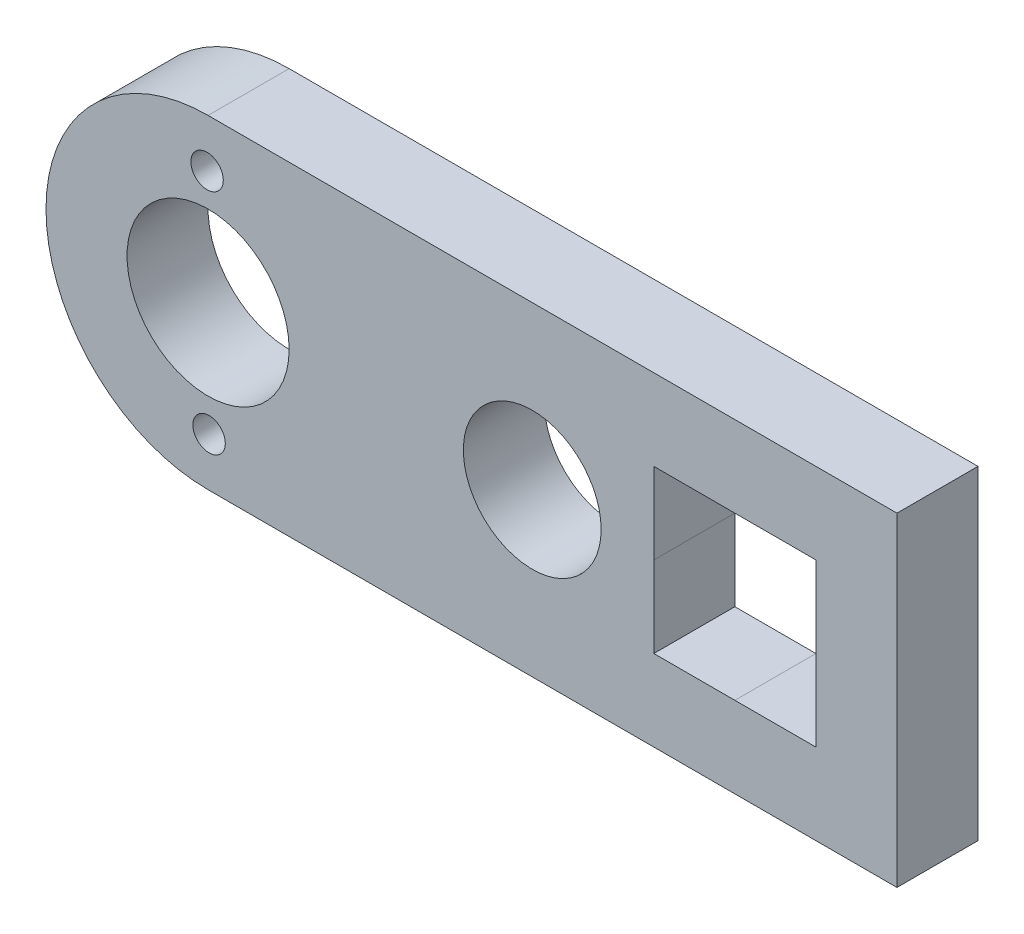
SolidWorks part; units mm, degrees
ref_plane "Front Plane" through (0, 0, 0) normal (0, 0, 1) x (1, 0, 0)
ref_plane "Top Plane" through (0, 0, 0) normal (0, 1, 0) x (1, 0, 0)
ref_plane "Right Plane" through (0, 0, 0) normal (1, 0, 0) x (0, 0, -1)
sketch "Sketch1" plane through (0, 0, 0) normal (0, 0, 1) x (1, 0, 0)
  line L0 (0, 10) -> (42.5, 10)
  line L1 (0, -10) -> (42.5, -10)
  line L2 (42.5, 10) -> (42.5, -10)
  line L3 (20, 5) -> (20, -5) construction
  line L4 (27.5, 5) -> (32.5, 5)
  line L5 (27.5, 5) -> (27.5, 0)
  line L6 (27.5, 0) -> (32.5, 0)
  line L7 (32.5, 5) -> (32.5, 0)
  line L8 (27.5, 5) -> (32.5, 0) construction
  line L9 (27.5, 0) -> (32.5, 5) construction
  line L10 (27.5, 0) -> (32.5, 0)
  line L11 (27.5, 0) -> (27.5, -5)
  line L12 (27.5, -5) -> (32.5, -5)
  line L13 (32.5, 0) -> (32.5, -5)
  line L14 (27.5, 0) -> (32.5, -5) construction
  line L15 (27.5, -5) -> (32.5, 0) construction
  line L16 (32.5, -5) -> (32.5, 5)
  line L17 (32.5, -5) -> (37.5, -5)
  line L18 (32.5, 5) -> (37.5, 5)
  line L19 (37.5, -5) -> (37.5, 5)
  arc A1 (0, 10) -> (0, -10) centre (0, 0) ccw
  circle A3 centre (20, 0) radius 4.25
  point P8 (30, 2.5)
  point P13 (30, -2.5)
  circle B0 centre (0, 0) radius 5
  circle B1 centre (7, 0.0625) radius 1
  circle B2 centre (0.0625, -7) radius 1
  circle B3 centre (-7, -0.0625) radius 1
  circle B4 centre (-0.0625, 7) radius 1
  dimension "D2" = 20
  dimension "D3" = 8.5
  dimension "D5" = 20
  dimension "D7" = 22.5
  dimension "D9" = 10
  dimension "D4" = 5
  dimension "D6" = 5
  dimension "D8" = 10
  dimension "D10" = 5
  dimension "D11" = 42.5
sketch_block_instance "Block1-1"
sketch_block "Block1" parameters "D1"=2, "D2"=10
extrude "Boss-Extrude1" add sketch "Sketch1" along normal blind 5
sketch "Sketch2" plane through (0, 0, 0) normal (0, 0, -1) x (-1, 0, 0)
  circle A0 centre (7, -0.0625) radius 1
  circle A1 centre (-7, 0.0625) radius 1.224
extrude "Boss-Extrude2" add sketch "Sketch2" against normal blind 5 contours A0
